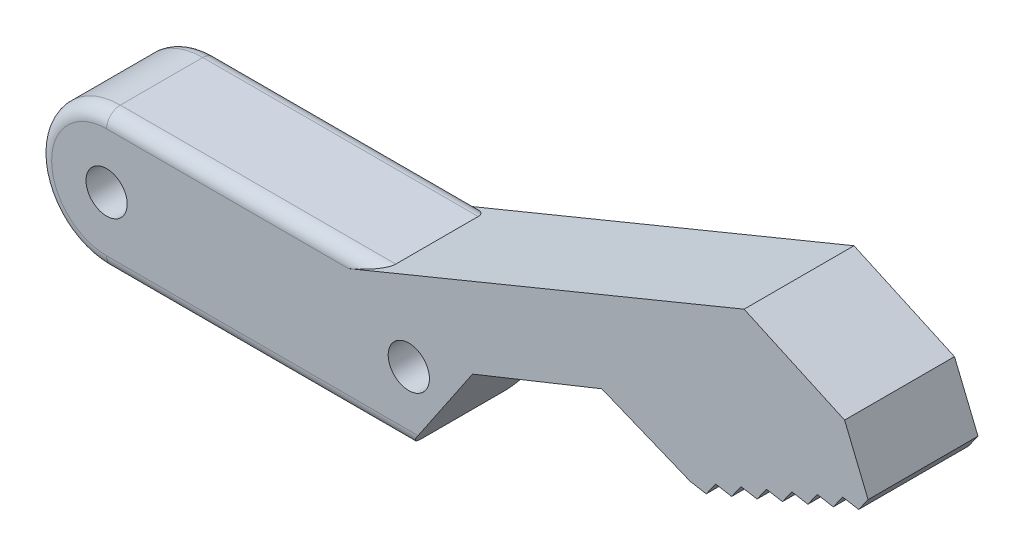
SolidWorks part; units mm, degrees
ref_plane "Front Plane" through (0, 0, 0) normal (0, 0, 1) x (1, 0, 0)
ref_plane "Top Plane" through (0, 0, 0) normal (0, 1, 0) x (1, 0, 0)
ref_plane "Right Plane" through (0, 0, 0) normal (1, 0, 0) x (0, 0, -1)
sketch "Sketch1" plane through (0, 0, 0) normal (0, 0, 1) x (1, 0, 0)
  line L0 (0, 0) -> (22, 0) construction
  line L1 (0, 5) -> (22, 5)
  line L2 (0, -5) -> (22, -5)
  line L3 (20.05, 5) -> (23.9914, -4.5863) construction
  line L4 (20.05, 5) -> (51.4959, 17.929) construction
  line L5 (23.9914, -4.5863) -> (55.4373, 8.3426) construction
  line L6 (51.4959, 17.929) -> (55.4373, 8.3426) construction
  line L7 (20.05, 5) -> (46.409, 15.8375)
  line L8 (46.409, 15.8375) -> (53.7261, 12.5046)
  line L9 (53.7261, 12.5046) -> (55.4373, 8.3426)
  line L10 (55.4373, 8.3426) -> (46.1885, 4.54) construction
  line L11 (46.1885, 4.54) -> (45.5032, 3.5771)
  line L12 (36.0496, 5.6382) -> (26.6403, 1.8622)
  line L13 (46.1885, 4.54) -> (47.3529, 4.3376)
  line L14 (47.3529, 4.3376) -> (48.0382, 5.3005)
  line L15 (47.3529, 4.3376) -> (54.752, 7.3797) construction
  line L16 (48.0382, 5.3005) -> (49.2027, 5.0981)
  line L17 (49.2027, 5.0981) -> (49.888, 6.0611)
  line L18 (49.888, 6.0611) -> (51.0524, 5.8587)
  line L19 (51.0524, 5.8587) -> (51.7378, 6.8216)
  line L20 (51.7378, 6.8216) -> (52.9022, 6.6192)
  line L21 (52.9022, 6.6192) -> (53.5875, 7.5821)
  line L22 (53.5875, 7.5821) -> (54.752, 7.3797)
  line L23 (54.752, 7.3797) -> (55.4373, 8.3426)
  line L24 (26.6403, 1.8622) -> (22, -5)
  line L25 (45.5032, 3.5771) -> (44.3387, 3.7795)
  line L26 (44.3387, 3.7795) -> (43.6534, 2.8165)
  line L27 (43.6534, 2.8165) -> (42.489, 3.019)
  line L28 (42.489, 3.019) -> (36.0496, 5.6382)
  arc A0 (0, 5) -> (0, -5) centre (0, 0) ccw
  arc A1 (22, -5) -> (22, 5) centre (22, 0) ccw
  circle A2 centre (0, 0) radius 1.5
  circle A3 centre (22, 0) radius 1.5
  point P3 (11, 0)
  point P21 (0, 0)
  point P36 (39.7411, 7.1527)
  dimension "D2" = 10
  dimension "D11" = 3
  dimension "D1" = 22
  dimension "D3" = 157.65
  dimension "D4" = 1.95
  dimension "D5" = 34
  dimension "D6" = 2
  dimension "D7" = 10
  dimension "D8" = 4.5
  dimension "D9" = 5.5
  dimension "D10" = 136
  dimension "D12" = 2
  dimension "D13" = 0.63
  dimension "D14" = 8
  dimension "D15" = 2
  dimension "D16" = 10.1387
extrude "Boss-Extrude1" add sketch "Sketch1" along normal blind 8
fillet "Fillet1" radius 1 6 edges at (10.025, 5, 0) (10.025, 5, 8) (11, -5, 0) (11, -5, 8) (-5, 0, 0) (-5, 0, 8)
